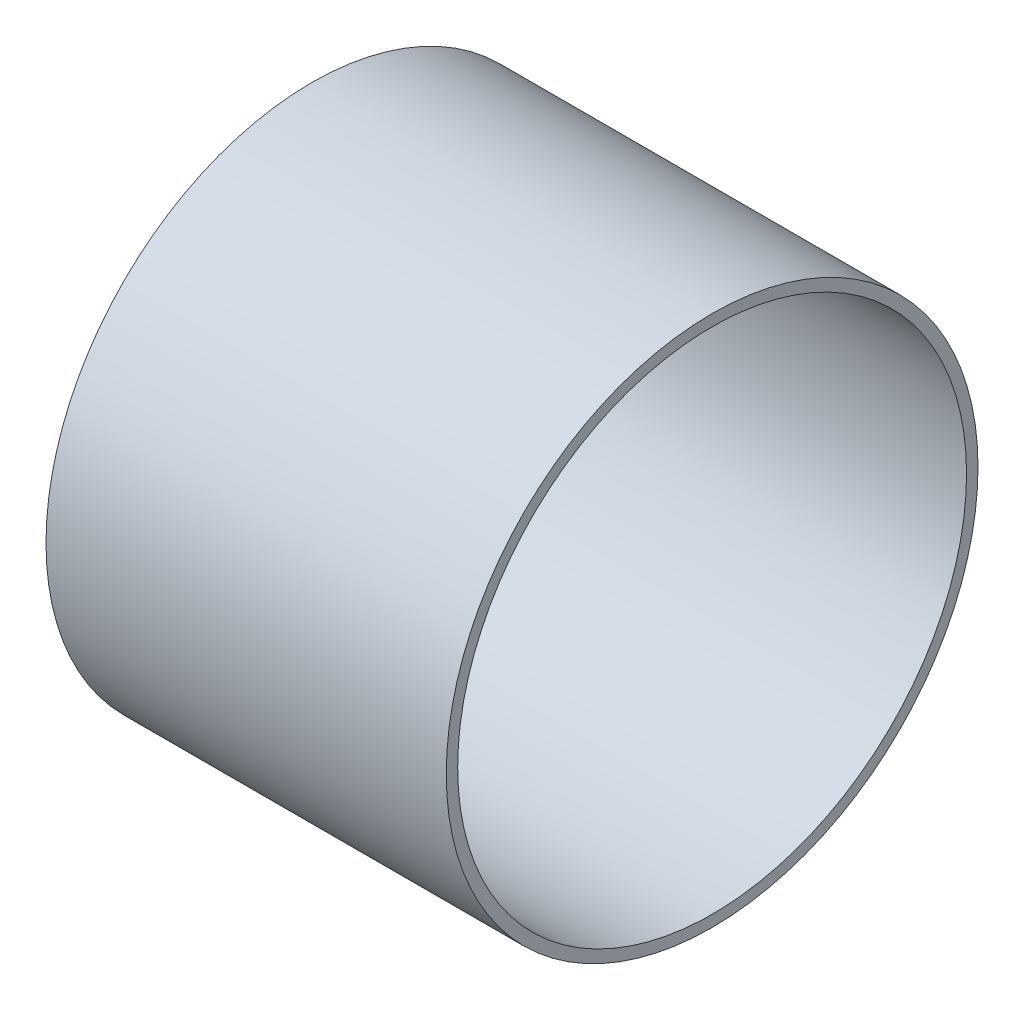
SolidWorks part; units mm, degrees
ref_plane "Plan de face" through (0, 0, 0) normal (0, 0, 1) x (1, 0, 0)
ref_plane "Plan de dessus" through (0, 0, 0) normal (0, 1, 0) x (1, 0, 0)
ref_plane "Plan de droite" through (0, 0, 0) normal (1, 0, 0) x (0, 0, -1)
sketch "Esquisse1" plane through (0, 0, 0) normal (0, 0, 1) x (1, 0, 0)
  line L0 (-29.9251, 0) -> (34.3758, 0) construction
  line L1 (-14, 17.8) -> (14, 17.8)
  line L2 (14, 17.8) -> (14, 18.6)
  line L3 (14, 18.6) -> (-14, 18.6)
  line L4 (-14, 18.6) -> (-14, 17.8)
  line L5 (0, 17.8) -> (0, 0) construction
  dimension "D1" = 37.2
  dimension "D2" = 35.6
  dimension "D3" = 28
revolve "Révolution1" add sketch "Esquisse1" angle 360 about L0
